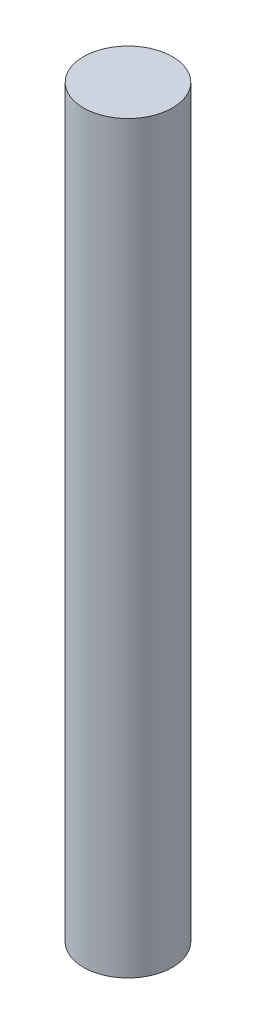
SolidWorks part; units mm, degrees
ref_plane "Front Plane" through (0, 0, 0) normal (0, 0, 1) x (1, 0, 0)
ref_plane "Top Plane" through (0, 0, 0) normal (0, 1, 0) x (1, 0, 0)
ref_plane "Right Plane" through (0, 0, 0) normal (1, 0, 0) x (0, 0, -1)
sketch "Sketch1" plane through (0, 0, 0) normal (0, 1, 0) x (1, 0, 0)
  circle A0 centre (0, 0) radius 8
  dimension "D1" = 16
extrude "Boss-Extrude1" add sketch "Sketch1" along normal blind 134
